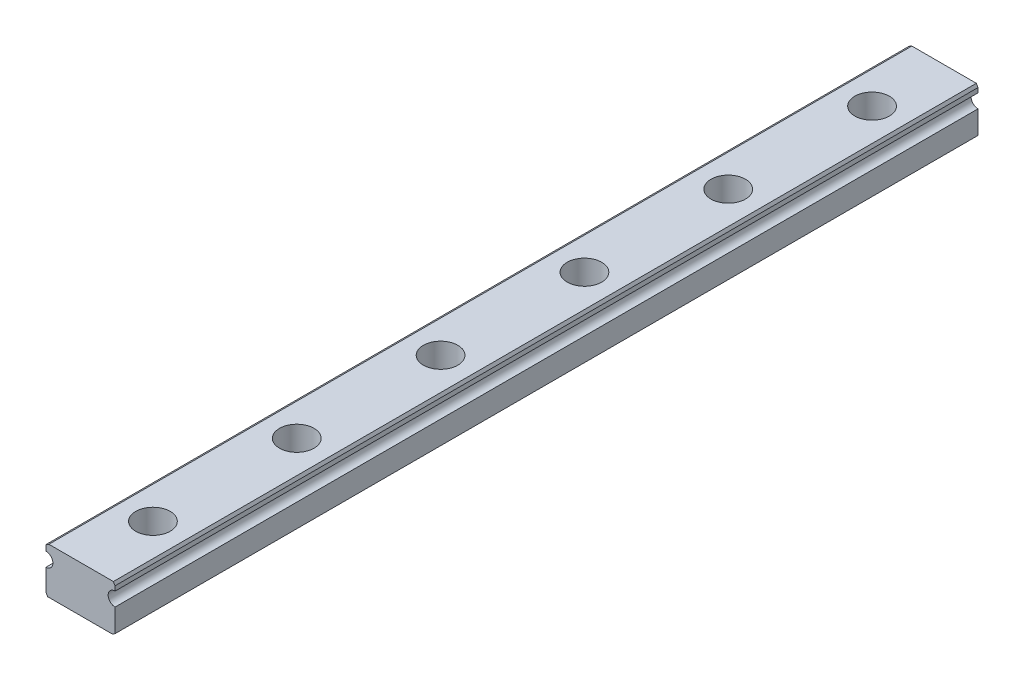
SolidWorks part; units mm, degrees
ref_plane "Front Plane" through (0, 0, 0) normal (0, 0, 1) x (1, 0, 0)
ref_plane "Top Plane" through (0, 0, 0) normal (0, 1, 0) x (1, 0, 0)
ref_plane "Right Plane" through (0, 0, 0) normal (1, 0, 0) x (0, 0, -1)
sketch "Sketch1" plane through (0, 0, 0) normal (0, 0, 1) x (1, 0, 0)
  line L0 (0, 4) -> (0, -4) construction
  line L1 (-6, -4) -> (6, -4)
  line L2 (-6, -4) -> (-6, 0.3)
  line L3 (-6, 4) -> (6, 4)
  line L4 (6, -4) -> (6, 0.3)
  line L5 (-6, -4) -> (6, 4) construction
  line L6 (-6, 4) -> (6, -4) construction
  line L7 (-6, 2.7) -> (-6, 4)
  line L8 (6, 2.7) -> (6, 4)
  arc A0 (-6, 0.3) -> (-6, 2.7) centre (-6, 1.5) ccw
  arc A1 (6, 0.3) -> (6, 2.7) centre (6, 1.5) cw
  point P0 (0, 0)
  dimension "D3" = 2.5
  dimension "D4" = 2.4
  dimension "D1" = 12
  dimension "D2" = 8
extrude "Boss-Extrude1" add sketch "Sketch1" along normal mid plane 150
chamfer "Chamfer1" distance 0.5 angle 30 4 edges at (-6, -4, 0) (6, -4, 0) (6, 4, 0) (-6, 4, 0)
sketch "Sketch2" plane through (0, 4, 0) normal (0, 1, 0) x (1, 0, 0)
  line L0 (0.1057, -75) -> (0, 0) construction
  line L1 (5.7113, -75) -> (-5.5, -75) construction
  circle A0 centre (0.0881, -62.5) radius 1.75
  dimension "D1" = 3.5
  dimension "D2" = 12.5
extrude "Cut-Extrude1" cut sketch "Sketch2" against normal up to next (8 mm away)
sketch "Sketch3" plane through (0, 4, 0) normal (0, 1, 0) x (1, 0, 0)
  circle A0 centre (0.0881, -62.5) radius 3
  dimension "D1" = 6
extrude "Cut-Extrude2" cut sketch "Sketch3" against normal blind 4.5
pattern_linear "LPattern1" count 6 spacing 25 along (0, 0, -1) of "Cut-Extrude1", "Cut-Extrude2"
